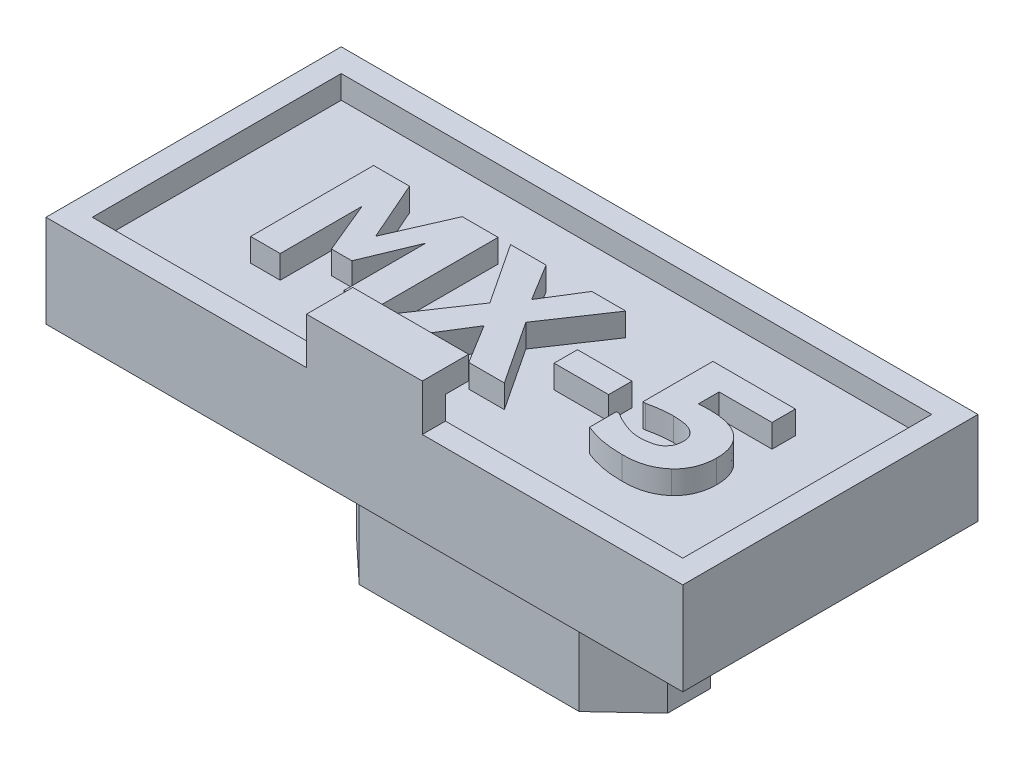
SolidWorks part; units mm, degrees
ref_plane "Front Plane" through (0, 0, 0) normal (0, 0, 1) x (1, 0, 0)
ref_plane "Top Plane" through (0, 0, 0) normal (0, 1, 0) x (1, 0, 0)
ref_plane "Right Plane" through (0, 0, 0) normal (1, 0, 0) x (0, 0, -1)
sketch "Sketch1" plane through (0, 0, 0) normal (0, 1, 0) x (1, 0, 0)
  line L1 (-6.985, 3.2385) -> (6.985, 3.2385)
  line L2 (-6.985, 3.2385) -> (-6.985, -3.2385)
  line L3 (-6.985, -3.2385) -> (6.985, -3.2385)
  line L4 (6.985, 3.2385) -> (6.985, -3.2385)
  line L5 (-6.985, 3.2385) -> (6.985, -3.2385) construction
  line L6 (-6.985, -3.2385) -> (6.985, 3.2385) construction
  point P0 (0, 0)
  dimension "D1" = 6.477
  dimension "D2" = 13.97
extrude "Boss-Extrude1" add sketch "Sketch1" along normal blind 1.524
sketch "Sketch2" plane through (0, 1.524, 0) normal (0, 1, 0) x (1, 0, 0)
  line L0 (-6.985, -3.2385) -> (6.985, -3.2385) construction
  line L1 (-1.27, -2.7305) -> (1.27, -2.7305)
  line L2 (-1.27, -2.7305) -> (-1.27, -3.2385)
  line L3 (-1.27, -3.2385) -> (1.27, -3.2385)
  line L4 (1.27, -2.7305) -> (1.27, -3.2385)
  line L5 (-1.27, -2.7305) -> (1.27, -3.2385) construction
  line L6 (-1.27, -3.2385) -> (1.27, -2.7305) construction
  point P0 (0, -2.9845)
  point P7 (0, 0)
  dimension "D1" = 0.508
  dimension "D2" = 2.54
extrude "Boss-Extrude2" add sketch "Sketch2" along normal blind 1.016
sketch "Sketch3" plane through (0, 2.54, 0) normal (0, 1, 0) x (1, 0, 0)
  line L1 (-1.27, -2.2225) -> (1.27, -2.2225)
  line L2 (-1.27, -2.2225) -> (-1.27, -3.2385)
  line L3 (-1.27, -3.2385) -> (1.27, -3.2385)
  line L4 (1.27, -2.2225) -> (1.27, -3.2385)
  line L5 (-1.27, -2.2225) -> (1.27, -3.2385) construction
  line L6 (-1.27, -3.2385) -> (1.27, -2.2225) construction
  line L11 (-1.27, -2.7305) -> (-1.27, -3.2385) construction
  point P0 (0, -2.7305)
  point P5 (-4.3154, -0.5366)
  point P6 (1.27, -2.7305)
extrude "Boss-Extrude3" add sketch "Sketch3" along normal blind 0.508
sketch "Sketch4" plane through (0, 1.524, 0) normal (0, 1, 0) x (1, 0, 0)
  line L0 (-6.477, 2.7305) -> (6.477, 2.7305)
  line L1 (-6.985, 3.2385) -> (6.985, 3.2385)
  line L2 (-6.985, 3.2385) -> (-6.985, -3.2385)
  line L3 (-6.985, -3.2385) -> (6.985, -3.2385)
  line L4 (6.985, 3.2385) -> (6.985, -3.2385)
  line L5 (6.477, 2.7305) -> (6.477, -2.7305)
  line L6 (-6.477, -2.7305) -> (6.477, -2.7305)
  line L7 (-6.477, 2.7305) -> (-6.477, -2.7305)
  point P5 (0, 0)
  line M9 (1.27, -2.7305) -> (1.27, -3.2385)
  line M10 (1.27, -3.2385) -> (6.985, -3.2385)
  line M11 (6.985, -3.2385) -> (6.985, 3.2385)
  line M12 (6.985, 3.2385) -> (-6.985, 3.2385)
  line M13 (-6.985, 3.2385) -> (-6.985, -3.2385)
  line M14 (-6.985, -3.2385) -> (-1.27, -3.2385)
  line M15 (-1.27, -3.2385) -> (-1.27, -2.7305)
  dimension "D1" = 0.508
extrude "Boss-Extrude4" add sketch "Sketch4" along normal blind 0.508 contours L7 L0 L5 L6 M9 M10 M11 M12 M13 M14 M15
sketch "Sketch5" plane through (0, 1.524, 0) normal (0, 1, 0) x (1, 0, 0)
  line L0 (-6.985, -3.2385) -> (-1.27, -3.2385) construction
  line L1 (-6.985, 3.2385) -> (-6.985, -3.2385) construction
  text T0 "<b>MX-5</b>"
  point P1 (-4.2133, -1.5665)
  point P2 (-4.619, -1.121)
  point P3 (-5.23, -1.3064)
  dimension "D1" = 1.8796
  dimension "D2" = 2.3368
extrude "Boss-Extrude5" add sketch "Sketch5" along normal blind 0.508
sketch "Sketch6" plane through (0, 0, 0) normal (0, -1, 0) x (1, 0, 0)
  line L0 (-3.4163, 0) -> (-2.413, 0.9398)
  line L1 (-2.413, 0.9398) -> (2.413, 0.9398)
  line L2 (-3.4163, 0) -> (-3.4163, -0.9398)
  line L3 (-3.4163, -0.9398) -> (-2.159, -0.9398)
  line L4 (3.4163, 0) -> (3.4163, -0.9398)
  line L5 (-2.6408, 0.7265) -> (3.4163, -0.9398) construction
  line L6 (-3.4163, -0.9398) -> (2.6408, 0.7265) construction
  line L7 (3.4163, 0) -> (2.413, 0.9398)
  line L8 (2.159, -0.9398) -> (3.4163, -0.9398)
  line L10 (-2.159, -0.9398) -> (-2.159, -0.0762)
  line L11 (-2.159, -0.0762) -> (2.159, -0.0762)
  line L12 (2.159, -0.9398) -> (2.159, -0.0762)
  point P0 (0, 0)
  point P4 (-3.4163, -0.4699)
  point P14 (0, -0.0762)
  point P16 (0, 0)
  dimension "D1" = 1.8796
  dimension "D2" = 6.8326
  dimension "D3" = 4.826
  dimension "D4" = 1.016
  dimension "D5" = 4.318
  dimension "D6" = 0.9398
  dimension "D7" = 0.0762
extrude "Boss-Extrude6" add sketch "Sketch6" along normal blind 3.81
